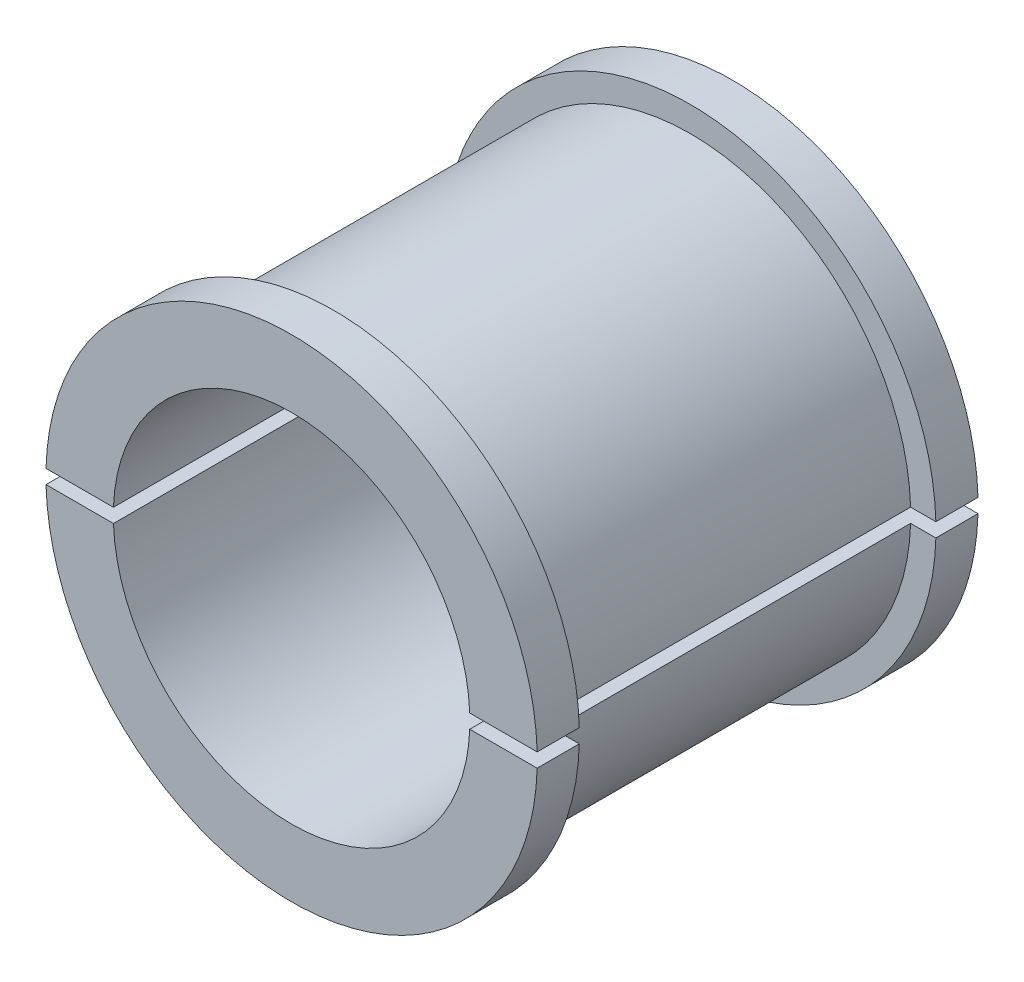
SolidWorks part; units mm, degrees
ref_plane "Front Plane" through (0, 0, 0) normal (0, 0, 1) x (1, 0, 0)
ref_plane "Top Plane" through (0, 0, 0) normal (0, 1, 0) x (1, 0, 0)
ref_plane "Right Plane" through (0, 0, 0) normal (1, 0, 0) x (0, 0, -1)
sketch "Sketch1" plane through (0, 0, 0) normal (1, 0, 0) x (0, 0, -1)
  line L0 (-67.8563, 0) -> (67.8563, 0) construction
  line L1 (-15.7, 12.7) -> (-15.7, 17.5)
  line L2 (-15.7, 17.5) -> (-12.7, 17.5)
  line L3 (-12.7, 17.5) -> (-12.7, 15.7)
  line L4 (-12.7, 15.7) -> (12.7, 15.7)
  line L5 (-15.7, 12.7) -> (15.7, 12.7)
  line L6 (0, 0) -> (0, 33.0552) construction
  line L7 (15.7, 12.7) -> (15.7, 17.5)
  line L8 (15.7, 17.5) -> (12.7, 17.5)
  line L9 (12.7, 17.5) -> (12.7, 15.7)
  point P14 (0, 15.7)
  dimension "D1" = 25.4
  dimension "D2" = 35
  dimension "D3" = 12.7
  dimension "D4" = 3
  dimension "D5" = 3
revolve "Revolve1" add sketch "Sketch1" angle 360 about L0
sketch "Sketch2" plane through (0, 0, 0) normal (0, 0, 1) x (1, 0, 0)
  line L1 (-21.0348, -0.5) -> (21.0348, -0.5)
  line L2 (-21.0348, -0.5) -> (-21.0348, 0.5)
  line L3 (-21.0348, 0.5) -> (21.0348, 0.5)
  line L4 (21.0348, -0.5) -> (21.0348, 0.5)
  line L5 (-21.0348, -0.5) -> (21.0348, 0.5) construction
  line L6 (-21.0348, 0.5) -> (21.0348, -0.5) construction
  point P0 (0, 0)
  dimension "D1" = 1
extrude "Cut-Extrude1" cut sketch "Sketch2" against normal through all and the other way through all
